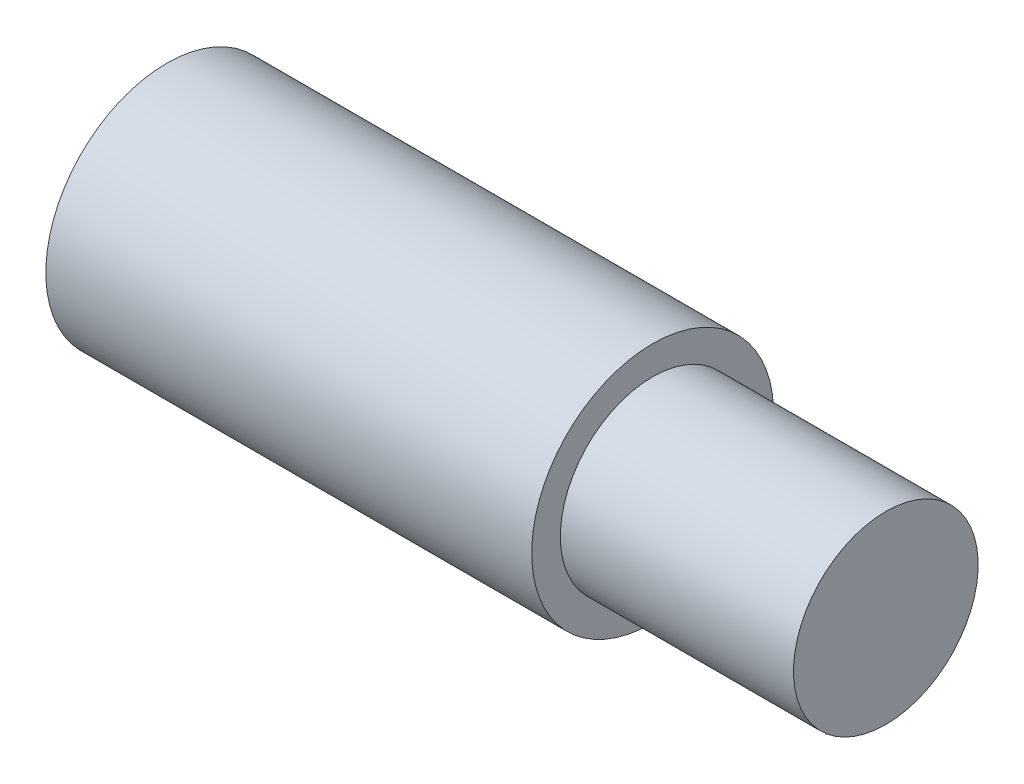
SolidWorks part; units mm, degrees
material "AISI 1015 Steel, Cold Drawn (SS)"
ref_plane "Front Plane" through (0, 0, 0) normal (0, 0, 1) x (1, 0, 0)
ref_plane "Top Plane" through (0, 0, 0) normal (0, 1, 0) x (1, 0, 0)
ref_plane "Right Plane" through (0, 0, 0) normal (1, 0, 0) x (0, 0, -1)
sketch "Sketch1" plane through (0, 0, 0) normal (0, 0, 1) x (1, 0, 0)
  line L0 (0, 3.1623) -> (12.7, 3.1623)
  line L1 (12.7, 3.1623) -> (12.7, 2.413)
  line L2 (12.7, 2.413) -> (18.796, 2.413)
  line L3 (18.796, 2.413) -> (18.796, 0)
  line L4 (18.796, 0) -> (0, 0)
  line L5 (0, 0) -> (0, 3.1623)
  line L6 (0, 0) -> (21.9374, 0) construction
  dimension "D1" = 6.096
  dimension "D2" = 12.7
  dimension "D3" = 3.1623
  dimension "D4" = 2.413
revolve "Revolve1" add sketch "Sketch1" angle 360 about L6
